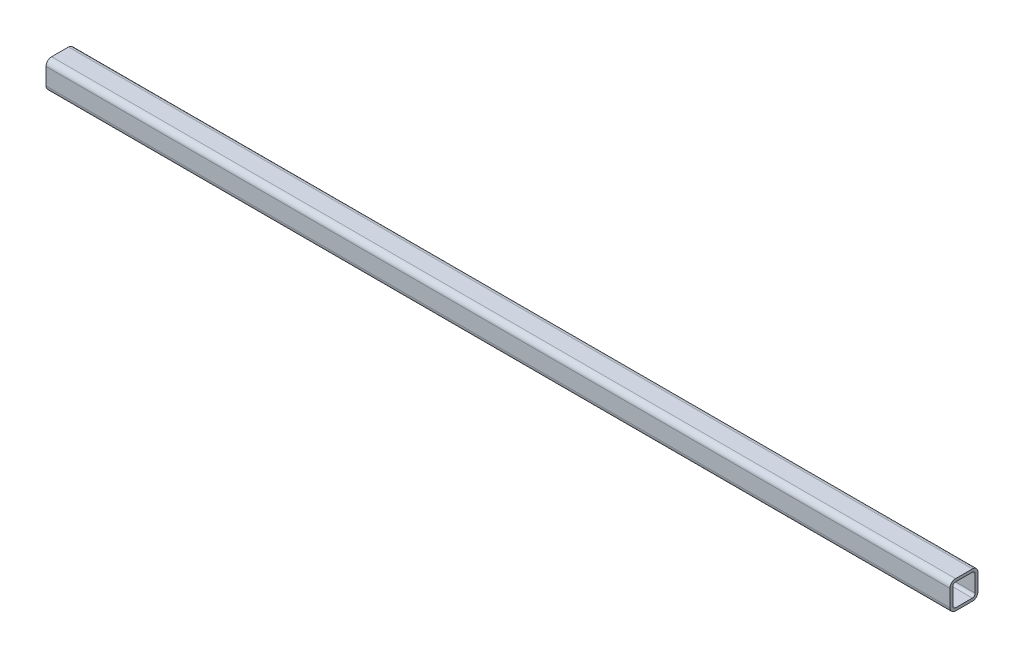
SolidWorks part; units mm, degrees
material "Beryllium"
ref_plane "Alzado" through (0, 0, 0) normal (0, 0, 1) x (1, 0, 0)
ref_plane "Planta" through (0, 0, 0) normal (0, 1, 0) x (1, 0, 0)
ref_plane "Vista lateral" through (0, 0, 0) normal (1, 0, 0) x (0, 0, -1)
sketch "Sketch1" plane through (0, 0, 0) normal (0, 1, 0) x (1, 0, 0)
  line L0 (-322.5, 0) -> (322.5, 0)
  point P4 (0, 0)
  dimension "D1" = 645
other "Square tube 20 X 20 X 2(1)"
ref_plane "Plane1" through (-322.5, 0, 0) normal (1, 0, 0) x (0, 0, -1)
sketch "Sketch11" plane through (-322.5, 0, 0) normal (1, 0, 0) x (0, 0, -1)
  line L0 (-6, -8) -> (6, -8)
  line L1 (-8, -6) -> (-8, 6)
  line L2 (6, 8) -> (-6, 8)
  line L3 (8, 6) -> (8, -6)
  line L4 (-6, -10) -> (6, -10)
  line L5 (-10, -6) -> (-10, 6)
  line L6 (6, 10) -> (-6, 10)
  line L7 (10, 6) -> (10, -6)
  arc A0 (10, 6) -> (6, 10) centre (6, 6) ccw
  arc A1 (6, -10) -> (10, -6) centre (6, -6) ccw
  arc A2 (-10, -6) -> (-6, -10) centre (-6, -6) ccw
  arc A3 (-6, 10) -> (-10, 6) centre (-6, 6) ccw
  arc A4 (-6, 8) -> (-8, 6) centre (-6, 6) ccw
  arc A5 (8, 6) -> (6, 8) centre (6, 6) ccw
  arc A6 (6, -8) -> (8, -6) centre (6, -6) ccw
  arc A7 (-8, -6) -> (-6, -8) centre (-6, -6) ccw
  point P0 (-10, 0)
  point P1 (10, 0)
  point P2 (0, 10)
  point P3 (0, -10)
  point P4 (0, 0)
  point P5 (-10, -10)
  point P6 (10, -10)
  point P7 (10, 10)
  point P8 (-10, 10)
  point P33 (0, 0)
  dimension "D1" = 4
  dimension "Thickness" = 2
  dimension "V_leg" = 20
